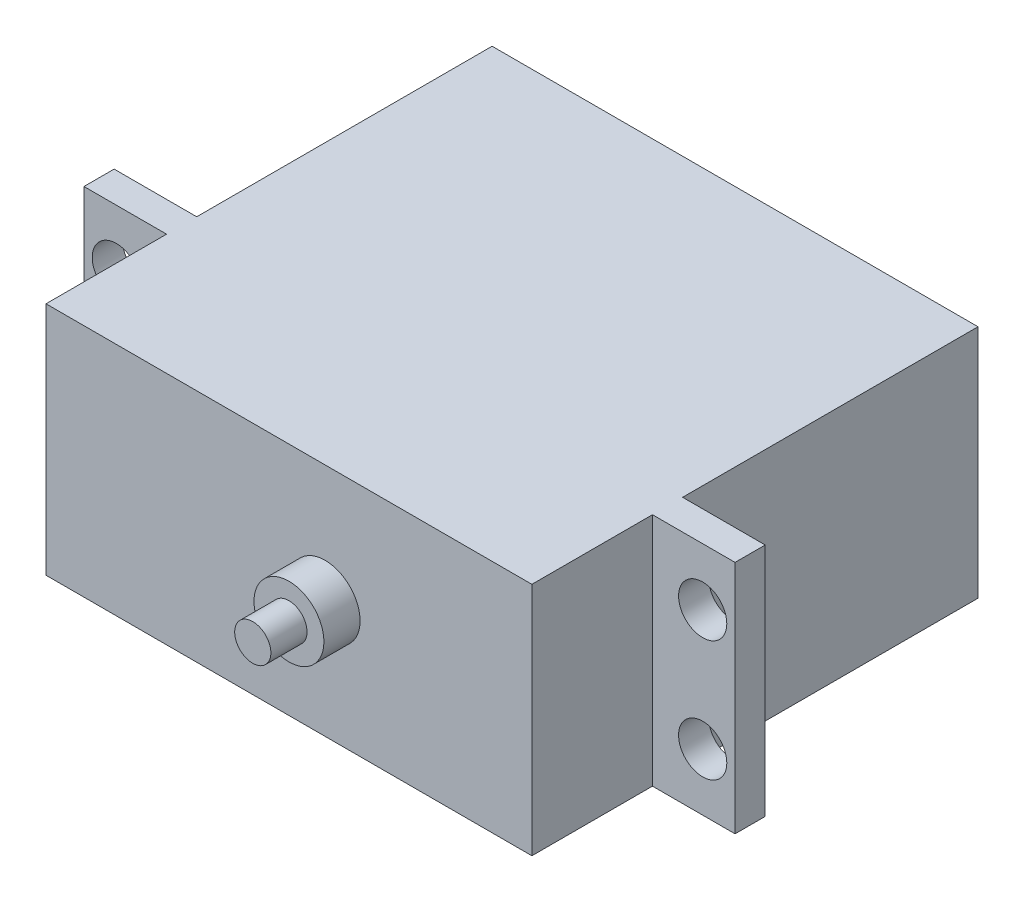
SolidWorks part; units mm, degrees
ref_plane "前视基准面" through (0, 0, 0) normal (0, 0, 1) x (1, 0, 0)
ref_plane "上视基准面" through (0, 0, 0) normal (0, 1, 0) x (1, 0, 0)
ref_plane "右视基准面" through (0, 0, 0) normal (1, 0, 0) x (0, 0, -1)
sketch "草图1" plane through (0, 0, 0) normal (0, 0, 1) x (1, 0, 0)
  line L1 (-20.15, 9.75) -> (20.15, 9.75)
  line L2 (-20.15, 9.75) -> (-20.15, -9.75)
  line L3 (-20.15, -9.75) -> (20.15, -9.75)
  line L4 (20.15, 9.75) -> (20.15, -9.75)
  line L5 (-20.15, 9.75) -> (20.15, -9.75) construction
  line L6 (-20.15, -9.75) -> (20.15, 9.75) construction
  point P0 (0, 0)
  dimension "D1" = 40.3
  dimension "D2" = 19.5
extrude "凸台-拉伸1" add sketch "草图1" along normal blind 37
sketch "草图2" plane through (0, 0, 37) normal (0, 0, 1) x (1, 0, 0)
  line L0 (20.15, -9.75) -> (20.15, 9.75) construction
  circle A0 centre (3, 0) radius 2.9
  point P4 (0, 0)
  dimension "D1" = 17.15
  dimension "D2" = 5.8
extrude "凸台-拉伸2" add sketch "草图2" along normal blind 3
sketch "草图3" plane through (0, 0, 40) normal (0, 0, 1) x (1, 0, 0)
  circle A0 centre (3, 0) radius 1.5
  dimension "D1" = 3
extrude "凸台-拉伸3" add sketch "草图3" along normal blind 3
ref_plane "基准面1" through (0, 0, 27) normal (0, 0, 1) x (1, 0, 0)
sketch "草图4" plane through (0, 0, 27) normal (0, 0, 1) x (1, 0, 0)
  line L0 (20.15, -9.75) -> (20.15, 9.75) construction
  line L1 (-27, 9.75) -> (27, 9.75)
  line L2 (-27, 9.75) -> (-27, -9.75)
  line L3 (-27, -9.75) -> (27, -9.75)
  line L4 (27, 9.75) -> (27, -9.75)
  line L5 (-27, 9.75) -> (27, -9.75) construction
  line L6 (-27, -9.75) -> (27, 9.75) construction
  point P0 (0, 0)
  dimension "D1" = 54
extrude "凸台-拉伸4" add sketch "草图4" against normal blind 2.5
sketch "草图5" plane through (0, 0, 37) normal (0, 0, 1) x (1, 0, 0)
  line L1 (-24.315, 5) -> (24.315, 5)
  line L2 (-24.315, 5) -> (-24.315, -5)
  line L3 (-24.315, -5) -> (24.315, -5)
  line L4 (24.315, 5) -> (24.315, -5)
  line L5 (-24.315, 5) -> (24.315, -5) construction
  line L6 (-24.315, -5) -> (24.315, 5) construction
  point P0 (0, 0)
  dimension "D1" = 10
  dimension "D2" = 48.63
hole_wizard "大小mm 暗销孔1" positions "草图6" profile "草图7" hole size "Ø4.0" standard "ISO"
sketch "草图6" plane through (0, 0, 27) normal (0, 0, 1) x (1, 0, 0)
  point P0 (-24.315, 5)
  point P3 (-24.315, -5)
  point P6 (24.315, -5)
  point P9 (24.315, 5)
sketch "草图7" plane through (-24.315, 5, 27) normal (1, 0, 0) x (0, -1, 0)
  line L0 (0, 0) -> (0, 8.7017)
  line L1 (0, 8.7017) -> (2, 7.5)
  line L2 (2, 7.5) -> (2, 0)
  line L5 (2, 0) -> (0, 0)
  line L10 (0, 8.7017) -> (-2, 7.5) construction
  line L11 (0, -6.35) -> (0, 107.95) construction
  dimension "孔直径" = 4
  dimension "孔深度" = 7.5
  dimension "导头角度" = 118
